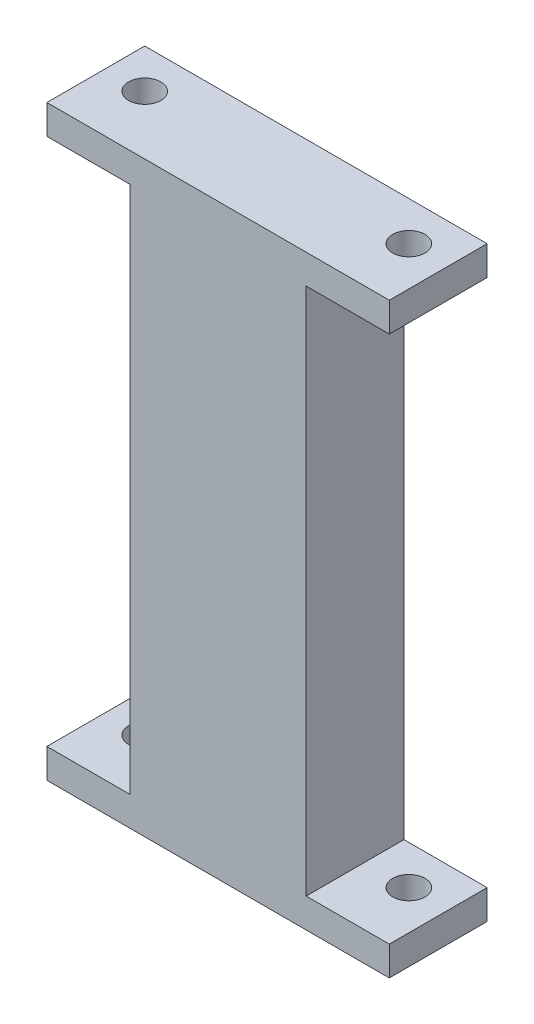
SolidWorks part; units mm, degrees
ref_plane "Front Plane" through (0, 0, 0) normal (0, 0, 1) x (1, 0, 0)
ref_plane "Top Plane" through (0, 0, 0) normal (0, 1, 0) x (1, 0, 0)
ref_plane "Right Plane" through (0, 0, 0) normal (1, 0, 0) x (0, 0, -1)
sketch "Sketch1" plane through (0, 0, 0) normal (0, 1, 0) x (1, 0, 0)
  line L1 (-17.5, -5) -> (17.5, -5)
  line L2 (-17.5, -5) -> (-17.5, 5)
  line L3 (-17.5, 5) -> (17.5, 5)
  line L4 (17.5, -5) -> (17.5, 5)
  line L5 (-17.5, -5) -> (17.5, 5) construction
  line L6 (-17.5, 5) -> (17.5, -5) construction
  point P0 (0, 0)
  dimension "D1" = 35
  dimension "D2" = 10
extrude "Boss-Extrude1" add sketch "Sketch1" along normal mid plane 3
sketch "Sketch2" plane through (0, 1.5, 0) normal (0, 1, 0) x (1, 0, 0)
  line L1 (-17.5, 5) -> (-17.5, -5) construction
  line L2 (0, 0) -> (-5.8518, 0) construction
  line L3 (0, 0) -> (0, -5.0733) construction
  circle A0 centre (-13.5, 1) radius 1.65
  circle A1 centre (13.5, 1) radius 1.65
  dimension "D1" = 3.3
  dimension "D2" = 1
  dimension "D3" = 4
extrude "Cut-Extrude1" cut sketch "Sketch2" against normal up to surface (3 mm away) up to face at (0, -1.5, 0)
sketch "Sketch3" plane through (0, 1.5, 0) normal (0, 1, 0) x (1, 0, 0)
  line L0 (-17.5, -5) -> (17.5, -5) construction
  line L1 (9, 5) -> (-9, 5)
  line L2 (9, 5) -> (9, -5)
  line L3 (9, -5) -> (-9, -5)
  line L4 (-9, 5) -> (-9, -5)
  line L5 (9, 5) -> (-9, -5) construction
  line L6 (9, -5) -> (-9, 5) construction
  point P0 (0, 0)
  dimension "D1" = 18
extrude "Boss-Extrude2" add sketch "Sketch3" along normal blind 54
ref_plane "Plane1" through (0, 28.5, 0) normal (0, 1, 0) x (1, 0, 0)
mirror "Mirror1" about plane through (0, 28.5, 0) normal (0, 1, 0) of "Cut-Extrude1", "Boss-Extrude1"
